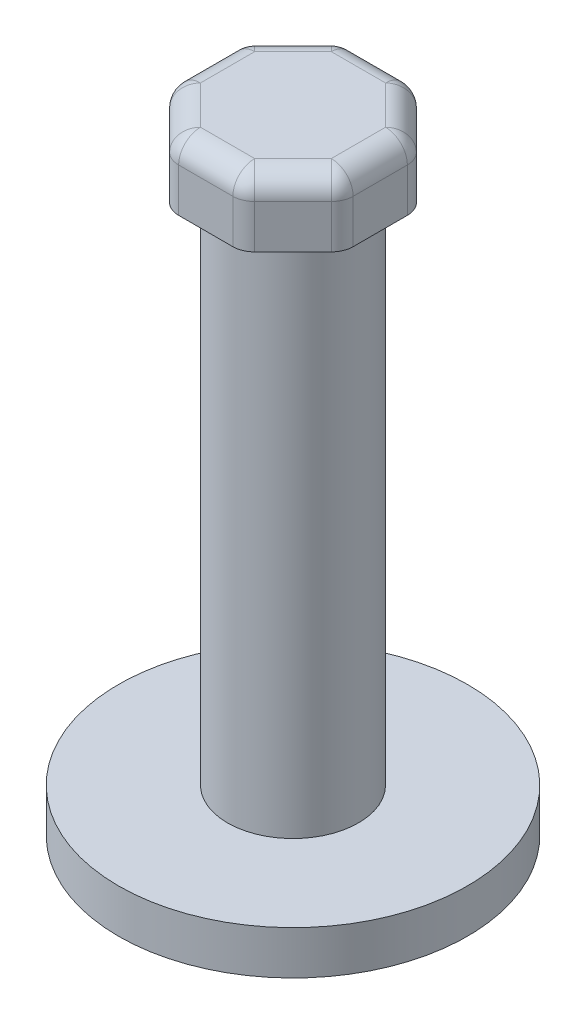
SolidWorks part; units mm, degrees
ref_plane "Front Plane" through (0, 0, 0) normal (0, 0, 1) x (1, 0, 0)
ref_plane "Top Plane" through (0, 0, 0) normal (0, 1, 0) x (1, 0, 0)
ref_plane "Right Plane" through (0, 0, 0) normal (1, 0, 0) x (0, 0, -1)
sketch "Sketch1" plane through (0, 0, 0) normal (0, 1, 0) x (1, 0, 0)
  circle A0 centre (0, 0) radius 10.16
  dimension "D1" = 20.32
extrude "Boss-Extrude1" add sketch "Sketch1" along normal blind 2.54
sketch "Sketch2" plane through (0, 2.54, 0) normal (0, 1, 0) x (1, 0, 0)
  circle A0 centre (0, 0) radius 3.81
  dimension "D1" = 7.62
extrude "Boss-Extrude2" add sketch "Sketch2" along normal blind 30.48
sketch "Sketch3" plane through (0, 33.02, 0) normal (0, 1, 0) x (1, 0, 0)
  line L1 (2.1042, 5.08) -> (-2.1042, 5.08)
  line L2 (-2.1042, 5.08) -> (-5.08, 2.1042)
  line L3 (-5.08, 2.1042) -> (-5.08, -2.1042)
  line L4 (-5.08, -2.1042) -> (-2.1042, -5.08)
  line L5 (-2.1042, -5.08) -> (2.1042, -5.08)
  line L6 (2.1042, -5.08) -> (5.08, -2.1042)
  line L7 (5.08, -2.1042) -> (5.08, 2.1042)
  line L8 (5.08, 2.1042) -> (2.1042, 5.08)
  circle A0 centre (0, 0) radius 5.08 construction
  dimension "D1" = 10.16
extrude "Boss-Extrude3" add sketch "Sketch3" along normal blind 3.81
fillet "Fillet1" radius 1.27 16 edges at (5.08, 36.83, 0) (3.5921, 36.83, -3.5921) (0, 36.83, -5.08) (-3.5921, 36.83, -3.5921) (-5.08, 36.83, 0) (3.5921, 36.83, 3.5921) (0, 36.83, 5.08) (-3.5921, 36.83, 3.5921) (5.08, 34.925, 2.1042) (2.1042, 34.925, 5.08) (-2.1042, 34.925, 5.08) (5.08, 34.925, -2.1042) (2.1042, 34.925, -5.08) (-5.08, 34.925, 2.1042) (-5.08, 34.925, -2.1042) (-2.1042, 34.925, -5.08)
sketch "Sketch4" plane through (5.08, 0, 0) normal (1, 0, 0) x (0, 0, -1)
  line L0 (0, 35.56) -> (0, 33.02) construction
  line L1 (1.5782, 35.56) -> (-1.5782, 35.56) construction
  line L2 (-3.81, 33.02) -> (3.81, 33.02) construction
  line L3 (-0.762, 33.655) -> (0.762, 33.655) construction
  line L4 (-0.762, 34.036) -> (0.762, 34.036)
  line L5 (-0.762, 33.274) -> (0.762, 33.274)
  line L6 (-1.5782, 34.29) -> (1.5782, 34.29) construction
  line L7 (-1.5782, 35.56) -> (-1.5782, 33.02) construction
  line L8 (1.5782, 33.02) -> (1.5782, 35.56) construction
  line L9 (-1.5782, 33.02) -> (1.5782, 33.02) construction
  arc A0 (-0.762, 34.036) -> (-0.762, 33.274) centre (-0.762, 33.655) ccw
  arc A1 (0.762, 33.274) -> (0.762, 34.036) centre (0.762, 33.655) ccw
  point P8 (0, 33.655)
  dimension "D1" = 1.524
  dimension "D2" = 0.762
  dimension "D3" = 0.635
  dimension "D4" = 0.635
